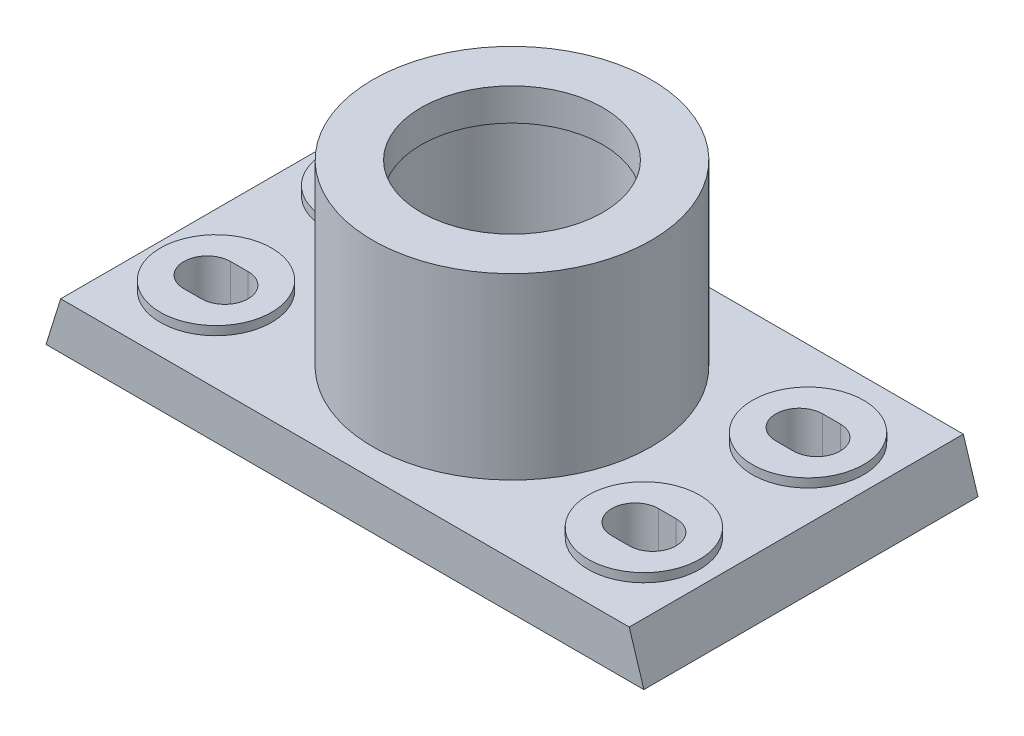
SolidWorks part; units mm, degrees
ref_plane "Front Plane" through (0, 0, 0) normal (0, 0, 1) x (1, 0, 0)
ref_plane "Top Plane" through (0, 0, 0) normal (0, 1, 0) x (1, 0, 0)
ref_plane "Right Plane" through (0, 0, 0) normal (1, 0, 0) x (0, 0, -1)
sketch "Sketch2" plane through (0, 0, 0) normal (0, 0, 1) x (1, 0, 0)
  line L0 (-145.7619, 0) -> (157.5205, 0) construction
  line L1 (0, 106.3818) -> (0, -101.0572) construction
  line L2 (-102, 0) -> (-97, 16)
  line L3 (-97, 16) -> (97, 16)
  line L4 (102, 0) -> (97, 16)
  line L5 (-102, 0) -> (102, 0)
  point P10 (0, 16)
  dimension "D1" = 204
  dimension "D2" = 16
  dimension "D3" = 5
extrude "Boss-Extrude1" add sketch "Sketch2" against normal blind 114
sketch "Sketch3" plane through (0, 0, 0) normal (0, -1, 0) x (1, 0, 0)
  line L0 (0, 26.2438) -> (0, -128.9097)
  line L1 (92, -104) -> (9.5, -104)
  line L2 (-92, -10) -> (-9.5, -10)
  line L3 (-92, -10) -> (-92, -104)
  line L4 (-92, -104) -> (-9.5, -104)
  line L5 (-9.5, -10) -> (-9.5, -104)
  line L6 (-92, -10) -> (-9.5, -104) construction
  line L7 (-92, -104) -> (-9.5, -10) construction
  line L8 (9.5, -10) -> (9.5, -104)
  line L9 (92, -10) -> (92, -104)
  line L10 (92, -10) -> (9.5, -10)
  point P2 (-50.75, -57)
  dimension "D1" = 82.5
  dimension "D2" = 10
  dimension "D3" = 47
  dimension "D4" = 57
  dimension "D5" = 9.5
extrude "Cut-Extrude1" cut sketch "Sketch3" against normal blind 3 contours L5 L2 L3 L4 | L9 L10 L8 L1
sketch "Sketch4" plane through (0, 16, 0) normal (0, 1, 0) x (1, 0, 0)
  line L0 (-76, 85) -> (-70, 85) construction
  line L1 (-76, 93) -> (-70, 93)
  line L2 (-76, 77) -> (-70, 77)
  line L3 (-102, 114) -> (-102, 0) construction
  line L4 (0, 0) -> (0, 136.1768)
  line L5 (-102, 57) -> (112.7959, 57)
  line L6 (76, 85) -> (70, 85) construction
  line L7 (76, 93) -> (70, 93)
  line L8 (76, 77) -> (70, 77)
  line L9 (76, 29) -> (70, 29) construction
  line L10 (76, 21) -> (70, 21)
  line L11 (76, 37) -> (70, 37)
  line L12 (-76, 29) -> (-70, 29) construction
  line L13 (-76, 21) -> (-70, 21)
  line L14 (-76, 37) -> (-70, 37)
  arc A0 (-76, 93) -> (-76, 77) centre (-76, 85) ccw
  arc A1 (-70, 77) -> (-70, 93) centre (-70, 85) ccw
  arc A2 (76, 93) -> (76, 77) centre (76, 85) cw
  arc A3 (70, 77) -> (70, 93) centre (70, 85) cw
  arc A4 (76, 21) -> (76, 37) centre (76, 29) ccw
  arc A5 (70, 37) -> (70, 21) centre (70, 29) ccw
  arc A6 (-76, 21) -> (-76, 37) centre (-76, 29) cw
  arc A7 (-70, 37) -> (-70, 21) centre (-70, 29) cw
  point P2 (-73, 85)
  point P7 (-102, 57)
  point P19 (73, 85)
  point P26 (73, 29)
  point P33 (-73, 29)
  dimension "D3" = 29
  dimension "D1" = 16
  dimension "D2" = 22
  dimension "D4" = 28
extrude "Cut-Extrude2" cut sketch "Sketch4" against normal through all contours L2 A1 L1 A0 | A3 L8 A2 L7 | A7 L14 A6 L13 | L11 A5 L10 A4
sketch "Sketch5" plane through (0, 16, 0) normal (0, 1, 0) x (1, 0, 0)
  line L0 (-102, 114) -> (-102, 0) construction
  line L1 (-102, 57) -> (135.4992, 57)
  line L2 (0, 0) -> (0, 134.5697)
  circle A0 centre (-73, 85) radius 19
  circle A1 centre (73, 85) radius 19
  circle A2 centre (-73, 29) radius 19
  circle A3 centre (73, 29) radius 19
  point P2 (-102, 57)
  line M1 (70, 37) -> (76, 37)
  arc M2 (76, 37) -> (76, 21) centre (76, 29) cw
  line M3 (76, 21) -> (70, 21)
  arc M4 (70, 21) -> (70, 37) centre (70, 29) cw
  line M5 (76, 77) -> (70, 77)
  arc M6 (70, 77) -> (70, 93) centre (70, 85) cw
  line M7 (70, 93) -> (76, 93)
  arc M8 (76, 93) -> (76, 77) centre (76, 85) cw
  line M9 (-70, 77) -> (-76, 77)
  arc M10 (-76, 77) -> (-76, 93) centre (-76, 85) cw
  line M11 (-76, 93) -> (-70, 93)
  arc M12 (-70, 93) -> (-70, 77) centre (-70, 85) cw
  line M17 (-76, 37) -> (-70, 37)
  arc M18 (-70, 37) -> (-70, 21) centre (-70, 29) cw
  line M19 (-70, 21) -> (-76, 21)
  arc M20 (-76, 21) -> (-76, 37) centre (-76, 29) cw
  dimension "D1" = 38
  dimension "D2" = 29
  dimension "D3" = 28
extrude "Boss-Extrude2" add sketch "Sketch5" along normal blind 3 contours A0 M12 M9 M10 M11 | A1 M8 M5 M6 M7 | A3 M4 M1 M2 M3 | A2 M20 M17 M18 M19
sketch "Sketch6" plane through (0, 16, 0) normal (0, 1, 0) x (1, 0, 0)
  circle A0 centre (0, 57) radius 31
  circle A1 centre (0, 57) radius 47.5
  dimension "D1" = 62
  dimension "D2" = 95
  dimension "D3" = 57
  dimension "D4" = 102
extrude "Boss-Extrude4" add sketch "Sketch6" along normal blind 61
ref_plane "Plane1" through (0, 0, -57) normal (0, 0, 1) x (1, 0, 0)
sketch "Sketch8" plane through (0, 0, -57) normal (0, 0, 1) x (1, 0, 0)
  line L0 (47.5, 77) -> (-47.5, 77) construction
  line L1 (-32.5, 66) -> (-29.5, 66)
  line L2 (-32.5, 66) -> (-32.5, 30.455)
  line L3 (-32.5, 30.455) -> (-29.5, 30.455)
  line L4 (-29.5, 66) -> (-29.5, 30.455)
  line L5 (0, 107.1062) -> (0, -5.921) construction
  dimension "D1" = 3
  dimension "D2" = 32.5
  dimension "D3" = 11
revolve "Cut-Revolve1" cut sketch "Sketch8" angle 360 about L5
sketch "Sketch9" plane through (0, 16, 0) normal (0, 1, 0) x (1, 0, 0)
  line L1 (-42.35, 57) -> (42.35, 57) construction
  circle A0 centre (-22, 57) radius 1.5
  dimension "D2" = 3
  dimension "D1" = 22
extrude "Cut-Extrude3" cut sketch "Sketch9" against normal blind 22
